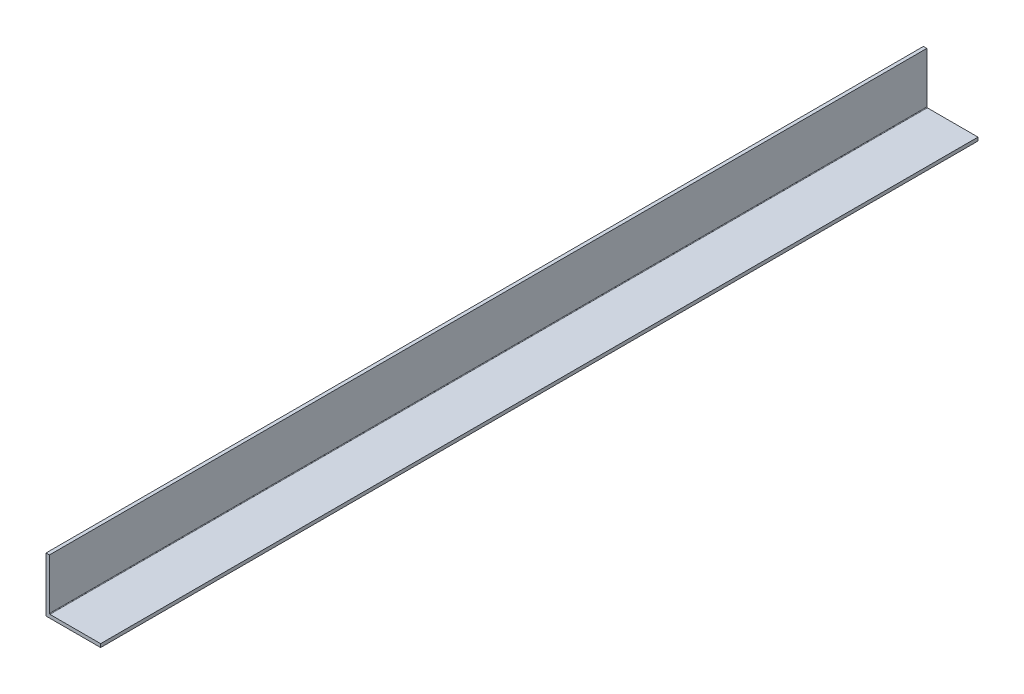
SolidWorks part; units mm, degrees
material "6061-T6 (SS)"
ref_plane "Front Plane" through (0, 0, 0) normal (0, 0, 1) x (1, 0, 0)
ref_plane "Top Plane" through (0, 0, 0) normal (0, 1, 0) x (1, 0, 0)
ref_plane "Right Plane" through (0, 0, 0) normal (1, 0, 0) x (0, 0, -1)
sketch "Sketch1" plane through (0, 0, 0) normal (0, 0, 1) x (1, 0, 0)
  line L0 (0, 25.4) -> (0, 0) construction
  line L1 (0, 0) -> (25.4, 0) construction
  line L2 (25.4, 0) -> (25.4, 1.5875) construction
  line L3 (25.4, 1.5875) -> (1.5875, 1.5875) construction
  line L4 (1.5875, 1.5875) -> (1.5875, 25.4) construction
  line L6 (1.5875, 25.4) -> (0, 25.4) construction
  arc A0 (1.5875, 1.8415) -> (1.8415, 1.5875) centre (1.8415, 1.8415) ccw construction
  point P4 (0, 0)
  dimension "Inside Corner Radius" = 0.254
  dimension "Outside Height" = 25.4
  dimension "Inside Height" = 23.8125
  dimension "Outside Width" = 25.4
  dimension "Inside Width" = 23.8125
  dimension "Wall Thickness" = 1.5875
  dimension "Shape" = 90
sketch "Sketch2" plane through (0, 0, 0) normal (1, 0, 0) x (0, 0, -1)
  line L0 (304.8, 0) -> (-304.8, 0) construction
  line L1 (-304.8, 25.4) -> (-304.8, 0) construction
  line L2 (304.8, 25.4) -> (304.8, 0) construction
  point P0 (-275.59, 0)
  point P4 (0, 0)
  point P6 (275.59, 0)
  dimension "D1" = 29.21
  dimension "D2" = 29.21
  dimension "D3" = 25.4
  dimension "Length" = 609.6
sketch "Sketch3" plane through (0, 0, 0) normal (0, 0, 1) x (1, 0, 0)
  line L0 (1.5875, 25.4) -> (0, 25.4)
  line L1 (0, 25.4) -> (0, 0)
  line L2 (0, 0) -> (25.4, 0)
  line L3 (25.4, 0) -> (25.4, 1.5875)
  line L4 (25.4, 1.5875) -> (1.5875, 1.5875)
  line L5 (1.5875, 1.5875) -> (1.5875, 25.4)
extrude "Boss-Extrude1" add sketch "Sketch3" along normal mid plane 609.6
fillet "Fillet1" radius 0.254 1 edges at (1.5875, 1.5875, 0)
sketch "Sketch4" plane through (0, 0, -304.8) normal (0, 0, -1) x (-1, 0, 0)
  line L6 (-1.5875, 25.4) -> (-1.5875, 1.8415)
  line L7 (-1.8415, 1.5875) -> (-25.4, 1.5875)
  line L8 (-25.4, 1.5875) -> (-25.4, 0)
  line L9 (-25.4, 0) -> (0, 0)
  line L10 (0, 0) -> (0, 25.4)
  line L11 (0, 25.4) -> (-1.5875, 25.4)
  line L12 (-1.5875, 25.4) -> (-1.5875, 1.8415)
  line L13 (-1.8415, 1.5875) -> (-25.4, 1.5875)
  line L14 (-25.4, 1.5875) -> (-25.4, 0)
  line L15 (-25.4, 0) -> (0, 0)
  line L16 (0, 0) -> (0, 25.4)
  line L17 (0, 25.4) -> (-1.5875, 25.4)
  arc A1 (-1.8415, 1.5875) -> (-1.5875, 1.8415) centre (-1.8415, 1.8415) ccw
  arc A2 (-1.8415, 1.5875) -> (-1.5875, 1.8415) centre (-1.8415, 1.8415) ccw
  dimension "D1" = 0
extrude "Cut-Extrude1" cut sketch "Sketch4" against normal offset from surface (201.6125 mm away) 407.9875 up to face at (7.9663, 7.9663, 304.8)
equation "\"D1@Boss-Extrude1\"=\"Length@Sketch2\""
equation "\"D1@Sketch2\" = \"Outside Width@Sketch1\" * 1.15"
equation "\"D2@Sketch2\"=\"D1@Sketch2\""
equation "\"D1@Fillet1\"=\"Inside Corner Radius@Sketch1\""
equation "\"D3@Sketch2\"=\"Outside Height@Sketch1\""
